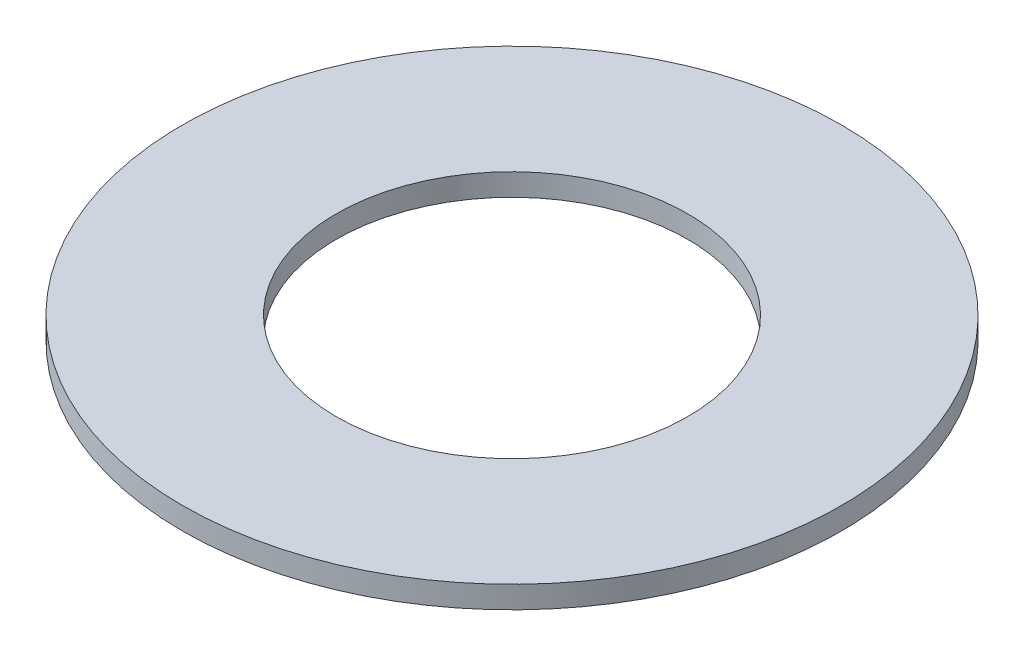
SolidWorks part; units mm, degrees
ref_plane "Front Plane" through (0, 0, 0) normal (0, 0, 1) x (1, 0, 0)
ref_plane "Top Plane" through (0, 0, 0) normal (0, 1, 0) x (1, 0, 0)
ref_plane "Right Plane" through (0, 0, 0) normal (1, 0, 0) x (0, 0, -1)
sketch "Sketch1" plane through (0, 0, 0) normal (0, 1, 0) x (1, 0, 0)
  circle A0 centre (0, 0) radius 6.35
  circle A1 centre (0, 0) radius 11.9062
  dimension "D1" = 12.7
  dimension "D2" = 23.8125
extrude "Boss-Extrude1" add sketch "Sketch1" along normal blind 0.8001
